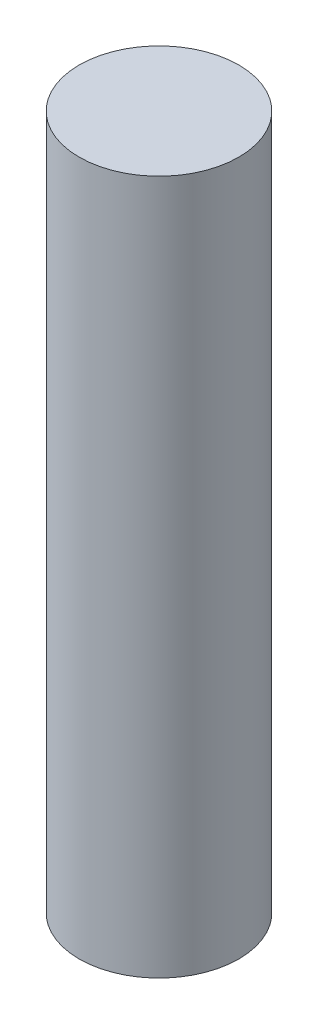
SolidWorks part; units mm, degrees
ref_plane "Front Plane" through (0, 0, 0) normal (0, 0, 1) x (1, 0, 0)
ref_plane "Top Plane" through (0, 0, 0) normal (0, 1, 0) x (1, 0, 0)
ref_plane "Right Plane" through (0, 0, 0) normal (1, 0, 0) x (0, 0, -1)
sketch "Sketch1" plane through (0, 0, 0) normal (0, 1, 0) x (1, 0, 0)
  circle A0 centre (0, 0) radius 5
extrude "Boss-Extrude1" add sketch "Sketch1" along normal blind 43.5
